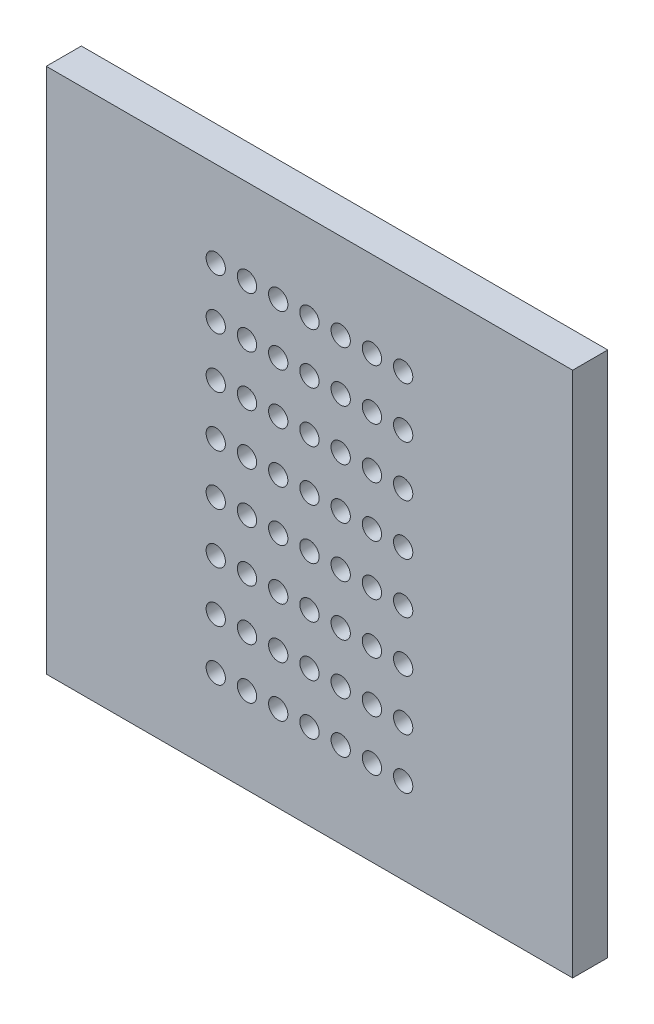
SolidWorks part; units mm, degrees
ref_plane "Plan de face" through (0, 0, 0) normal (0, 0, 1) x (1, 0, 0)
ref_plane "Plan de dessus" through (0, 0, 0) normal (0, 1, 0) x (1, 0, 0)
ref_plane "Plan de droite" through (0, 0, 0) normal (1, 0, 0) x (0, 0, -1)
sketch "Esquisse1" plane through (0, 0, 0) normal (0, 0, 1) x (1, 0, 0)
  line L1 (-15, -15) -> (15, -15)
  line L2 (-15, -15) -> (-15, 15)
  line L3 (-15, 15) -> (15, 15)
  line L4 (15, -15) -> (15, 15)
  line L5 (-15, -15) -> (15, 15) construction
  line L6 (-15, 15) -> (15, -15) construction
  point P0 (0, 0)
extrude "Base_Plate" add sketch "Esquisse1" along normal blind 2
sketch "Sketch_Perforations" plane through (0, 0, 2) normal (0, 0, 1) x (1, 0, 0)
  circle A0 centre (-5.34, -10.11) radius 0.55
  circle A1 centre (-5.34, -7.22) radius 0.55
  circle A2 centre (-5.34, -4.33) radius 0.55
  circle A3 centre (-5.34, -1.44) radius 0.55
  circle A4 centre (-5.34, 1.44) radius 0.55
  circle A5 centre (-5.34, 4.33) radius 0.55
  circle A6 centre (-5.34, 7.22) radius 0.55
  circle A7 centre (-5.34, 10.11) radius 0.55
  circle A8 centre (-3.56, -10.11) radius 0.55
  circle A9 centre (-3.56, -7.22) radius 0.55
  circle A10 centre (-3.56, -4.33) radius 0.55
  circle A11 centre (-3.56, -1.44) radius 0.55
  circle A12 centre (-3.56, 1.44) radius 0.55
  circle A13 centre (-3.56, 4.33) radius 0.55
  circle A14 centre (-3.56, 7.22) radius 0.55
  circle A15 centre (-3.56, 10.11) radius 0.55
  circle A16 centre (-1.78, -10.11) radius 0.55
  circle A17 centre (-1.78, -7.22) radius 0.55
  circle A18 centre (-1.78, -4.33) radius 0.55
  circle A19 centre (-1.78, -1.44) radius 0.55
  circle A20 centre (-1.78, 1.44) radius 0.55
  circle A21 centre (-1.78, 4.33) radius 0.55
  circle A22 centre (-1.78, 7.22) radius 0.55
  circle A23 centre (-1.78, 10.11) radius 0.55
  circle A24 centre (0, -10.11) radius 0.55
  circle A25 centre (0, -7.22) radius 0.55
  circle A26 centre (0, -4.33) radius 0.55
  circle A27 centre (0, -1.44) radius 0.55
  circle A28 centre (0, 1.44) radius 0.55
  circle A29 centre (0, 4.33) radius 0.55
  circle A30 centre (0, 7.22) radius 0.55
  circle A31 centre (0, 10.11) radius 0.55
  circle A32 centre (1.78, -10.11) radius 0.55
  circle A33 centre (1.78, -7.22) radius 0.55
  circle A34 centre (1.78, -4.33) radius 0.55
  circle A35 centre (1.78, -1.44) radius 0.55
  circle A36 centre (1.78, 1.44) radius 0.55
  circle A37 centre (1.78, 4.33) radius 0.55
  circle A38 centre (1.78, 7.22) radius 0.55
  circle A39 centre (1.78, 10.11) radius 0.55
  circle A40 centre (3.56, -10.11) radius 0.55
  circle A41 centre (3.56, -7.22) radius 0.55
  circle A42 centre (3.56, -4.33) radius 0.55
  circle A43 centre (3.56, -1.44) radius 0.55
  circle A44 centre (3.56, 1.44) radius 0.55
  circle A45 centre (3.56, 4.33) radius 0.55
  circle A46 centre (3.56, 7.22) radius 0.55
  circle A47 centre (3.56, 10.11) radius 0.55
  circle A48 centre (5.34, -10.11) radius 0.55
  circle A49 centre (5.34, -7.22) radius 0.55
  circle A50 centre (5.34, -4.33) radius 0.55
  circle A51 centre (5.34, -1.44) radius 0.55
  circle A52 centre (5.34, 1.44) radius 0.55
  circle A53 centre (5.34, 4.33) radius 0.55
  circle A54 centre (5.34, 7.22) radius 0.55
  circle A55 centre (5.34, 10.11) radius 0.55
extrude "Cut_Perforations" cut sketch "Sketch_Perforations" against normal blind 10
